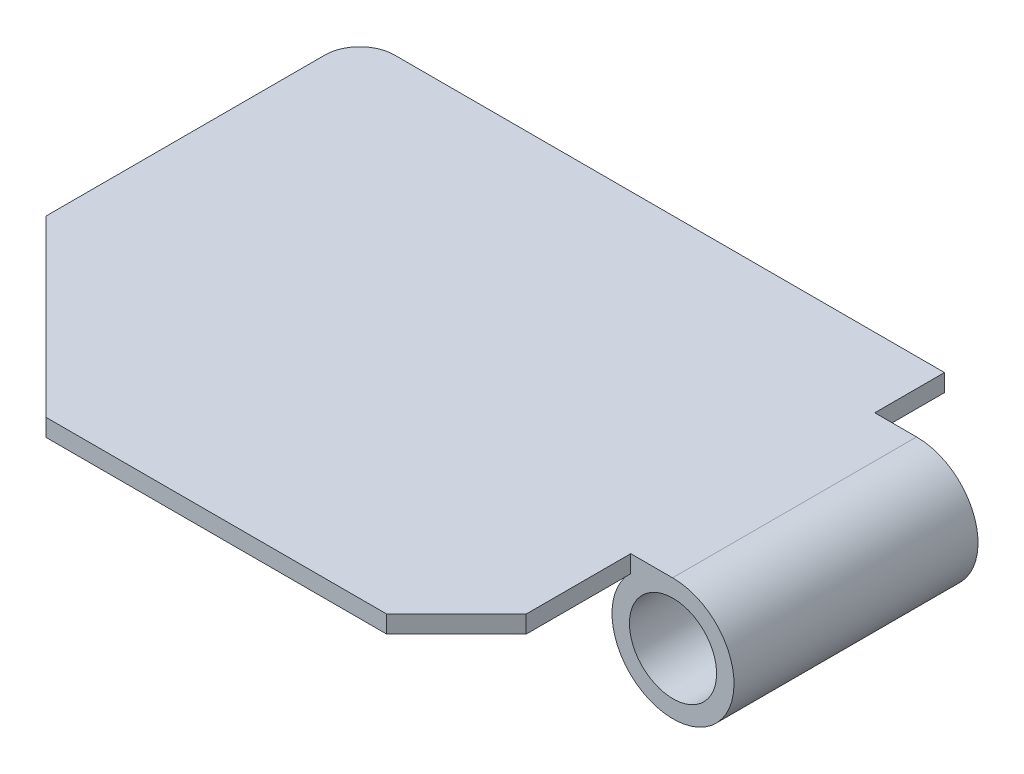
SolidWorks part; units mm, degrees
ref_plane "Front Plane" through (0, 0, 0) normal (0, 0, 1) x (1, 0, 0)
ref_plane "Top Plane" through (0, 0, 0) normal (0, 1, 0) x (1, 0, 0)
ref_plane "Right Plane" through (0, 0, 0) normal (1, 0, 0) x (0, 0, -1)
sketch "Sketch1" plane through (0, 0, 0) normal (0, 1, 0) x (1, 0, 0)
  line L0 (0, 0) -> (97.75, 0)
  line L1 (97.75, 0) -> (117.747, 19.997)
  line L2 (117.747, 19.997) -> (117.747, 49.997)
  line L3 (117.747, 49.997) -> (130.0005, 49.997)
  line L4 (130.0005, 49.997) -> (130.0005, 119.997)
  line L6 (117.7505, 119.997) -> (117.7505, 139.9995)
  line L7 (117.7505, 139.9995) -> (-39.9995, 139.9995)
  line L8 (-49.9995, 129.9995) -> (-49.9995, 49.9995)
  line L9 (-49.9995, 49.9995) -> (0, 0)
  line L10 (117.7505, 119.997) -> (130.0005, 119.997)
  arc A0 (-49.9995, 129.9995) -> (-39.9995, 139.9995) centre (-39.9995, 129.9995) cw
  dimension "D2" = 10
  dimension "D1" = 97.75
  dimension "D3" = 157.75
  dimension "D4" = 135
  dimension "D5" = 135
  dimension "D6" = 80
  dimension "D7" = 12.25
  dimension "D8" = 30
  dimension "D9" = 70
  dimension "D10" = 70.71
  dimension "D11" = 28.28
extrude "Boss-Extrude1" add sketch "Sketch1" against normal blind 5
ref_plane "Plane2" through (0, 0, -119.997) normal (0, 0, -1) x (-1, 0, 0)
sketch "Sketch3" plane through (0, 0, -119.997) normal (0, 0, -1) x (-1, 0, 0)
  line L0 (-130.0005, 0) -> (-130.0005, -34.999) construction
  circle A0 centre (-129.8713, -17.4995) radius 17.5
  circle A1 centre (-129.8713, -17.4995) radius 12.5
  dimension "D1" = 35
  dimension "D2" = 25
extrude "Boss-Extrude2" add sketch "Sketch3" against normal up to surface (70 mm away) up to face at (123.8737, -2.5, -49.997)
